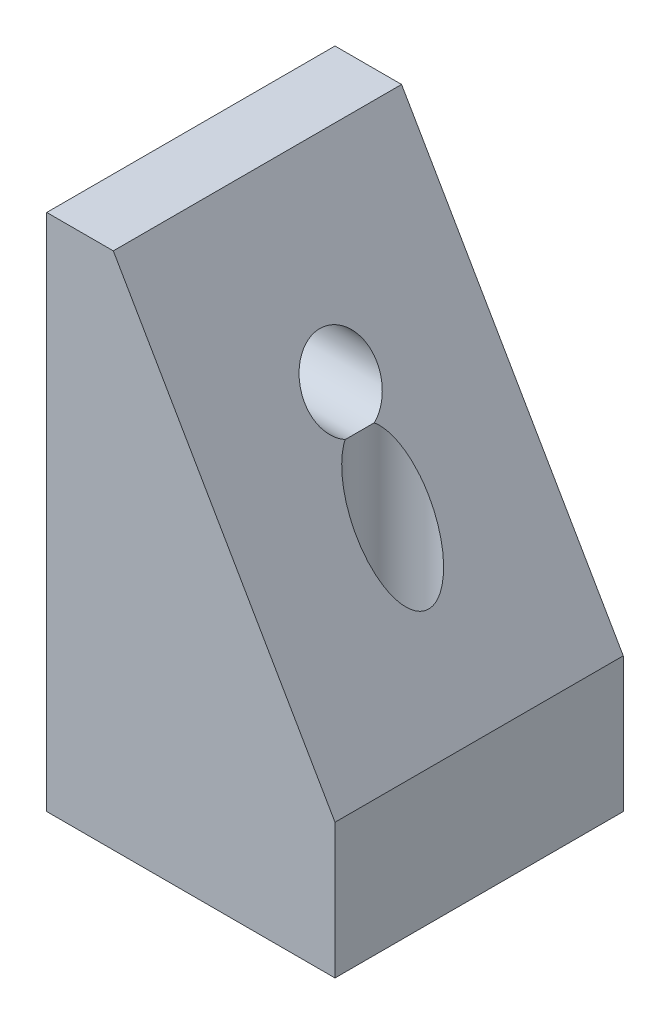
SolidWorks part; units mm, degrees
material "2024-T4"
ref_plane "Спереди" through (0, 0, 0) normal (0, 0, 1) x (1, 0, 0)
ref_plane "Сверху" through (0, 0, 0) normal (0, 1, 0) x (1, 0, 0)
ref_plane "Справа" through (0, 0, 0) normal (1, 0, 0) x (0, 0, -1)
sketch "Эскиз1" plane through (0, 0, 0) normal (0, 0, 1) x (1, 0, 0)
  line L0 (0, 0) -> (0, 18)
  line L1 (0, 18) -> (2.3094, 18)
  line L2 (2.3094, 18) -> (10, 4.6795)
  line L3 (10, 4.6795) -> (10, 0)
  line L4 (10, 0) -> (0, 0)
  dimension "D1" = 18
  dimension "D2" = 10
  dimension "D3" = 30
  dimension "D4" = 11
extrude "Бобышка-Вытянуть1" add sketch "Эскиз1" along normal blind 10
hole_wizard "Отверстие обработанное метчиком M31" positions "Эскиз3" profile "Эскиз2" tap size "M3" standard "DIN"
sketch "Эскиз3" plane through (0, 0, 0) normal (-1, 0, 0) x (0, 0, 1)
  line L2 (0, 18) -> (0, 0) construction
  line L3 (10, 0) -> (0, 0) construction
  point P0 (5, 13)
  dimension "D1" = 5
  dimension "D2" = 13
cosmetic thread "Отверстие резьбы2" parameters "D2"=3
sketch "Эскиз2" plane through (0, 13, 5) normal (0, 1, 0) x (0, 0, 1)
  line L0 (0, 0) -> (0, 5.1962)
  line L1 (0, 5.1962) -> (1.25, 5.1962)
  line L2 (1.25, 5.1962) -> (1.25, 0.2451)
  line L3 (1.25, 0.2451) -> (1.6, 0)
  line L5 (1.6, 0) -> (0, 0)
  line L6 (-1.25, 0.2451) -> (-1.6, 0) construction
  line L11 (0, -6.35) -> (0, 107.95) construction
  dimension "Диаметр проходного сверла" = 2.5
  dimension "Глубина проходного сверла" = 5.1962
  dimension "Диаметр передней зенковки" = 3.2
  dimension "Угол передней зенковки" = 110
hole_wizard "Отверстие обработанное метчиком M32" positions "Эскиз5" profile "Эскиз4" tap size "M3" standard "DIN" end condition through all
sketch "Эскиз5" plane through (0, 0, 0) normal (0, -1, 0) x (1, 0, 0)
  line L0 (0, 0) -> (10, 0) construction
  line L1 (0, 10) -> (0, 0) construction
  point P0 (7, 5)
  dimension "D1" = 5
  dimension "D2" = 7
sketch "Эскиз4" plane through (7, 0, 5) normal (1, 0, 0) x (0, 0, -1)
  line L0 (0, 0) -> (0, 18)
  line L1 (0, 18) -> (1.25, 18)
  line L2 (1.25, 18) -> (1.25, 0.2801)
  line L3 (1.25, 0.2801) -> (1.65, 0)
  line L5 (1.65, 0) -> (0, 0)
  line L6 (-1.25, 0.2801) -> (-1.65, 0) construction
  line L11 (0, -6.35) -> (0, 107.95) construction
  dimension "Диаметр проходного сверла" = 2.5
  dimension "Глубина проходного сверла" = 18
  dimension "Диаметр передней зенковки" = 3.3
  dimension "Угол передней зенковки" = 110
cosmetic thread "Отверстие резьбы3" parameters "D2"=3
